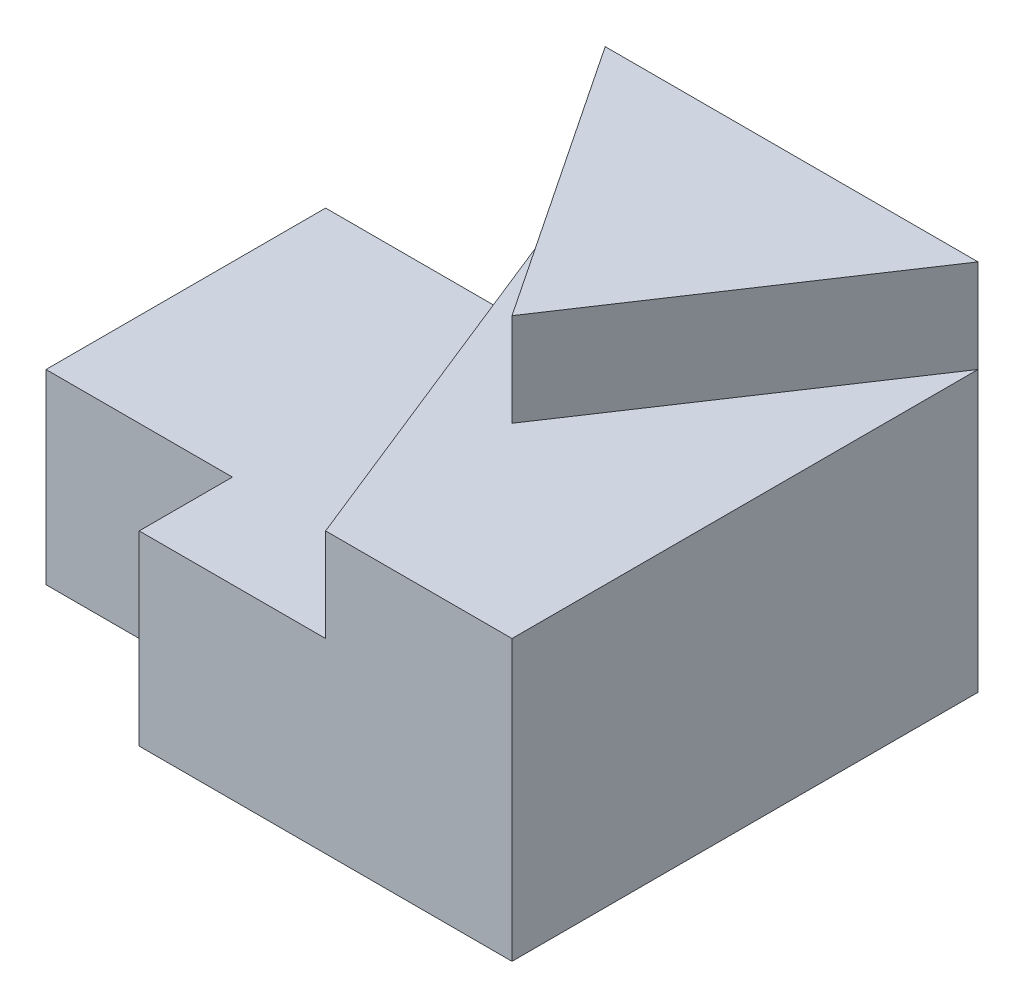
SolidWorks part; units mm, degrees
ref_plane "Front Plane" through (0, 0, 0) normal (0, 0, 1) x (1, 0, 0)
ref_plane "Top Plane" through (0, 0, 0) normal (0, 1, 0) x (1, 0, 0)
ref_plane "Right Plane" through (0, 0, 0) normal (1, 0, 0) x (0, 0, -1)
sketch "Sketch1" plane through (0, 0, 0) normal (0, 0, 1) x (1, 0, 0)
  line L0 (0, 0) -> (20, 0)
  line L1 (20, 0) -> (20, 20)
  line L2 (20, 20) -> (10, 20)
  line L3 (10, 20) -> (10, 10)
  line L4 (10, 10) -> (0, 10)
  line L5 (0, 10) -> (0, 0)
  dimension "D1" = 10
  dimension "D2" = 10
  dimension "D3" = 20
  dimension "D4" = 20
extrude "Boss-Extrude1" add sketch "Sketch1" along normal blind 25
sketch "Sketch2" plane through (0, 0, 0) normal (-1, 0, 0) x (0, 0, 1)
  line L0 (25, 0) -> (0, 0) construction
  line L1 (5, 0) -> (20, 0)
  line L2 (5, 0) -> (5, 10)
  line L3 (5, 10) -> (20, 10)
  line L4 (20, 0) -> (20, 10)
  line L5 (25, 10) -> (0, 10) construction
  line L6 (0, 10) -> (0, 0) construction
  dimension "D1" = 15
  dimension "D2" = 5
extrude "Boss-Extrude2" add sketch "Sketch2" along normal blind 10
sketch "Sketch3" plane through (10, 0, 0) normal (-1, 0, 0) x (0, 0, 1)
  line L1 (0, 10) -> (25, 10)
  line L2 (0, 10) -> (0, 20)
  line L3 (0, 20) -> (25, 20)
  line L4 (25, 10) -> (25, 20)
extrude "Boss-Extrude3" add sketch "Sketch3" along normal blind 10
sketch "Sketch5" plane through (0, 20, 0) normal (0, 1, 0) x (1, 0, 0)
  line L0 (0, 0) -> (0, -25)
  line L1 (0, -25) -> (20, -25)
  line L2 (20, -25) -> (20, 0)
  line L3 (20, 0) -> (10, -15)
  line L4 (10, -15) -> (0, 0)
  dimension "D1" = 15
  dimension "D2" = 10
extrude "Cut-Extrude1" cut sketch "Sketch5" against normal blind 5
sketch "Sketch6" plane through (0, 15, 0) normal (0, 1, 0) x (1, 0, 0)
  line L0 (0, -25) -> (10, -25)
  line L1 (0, -25) -> (20, -25) construction
  line L2 (10, -25) -> (0, 0)
  line L3 (0, 0) -> (0, -25)
extrude "Cut-Extrude2" cut sketch "Sketch6" against normal blind 5
